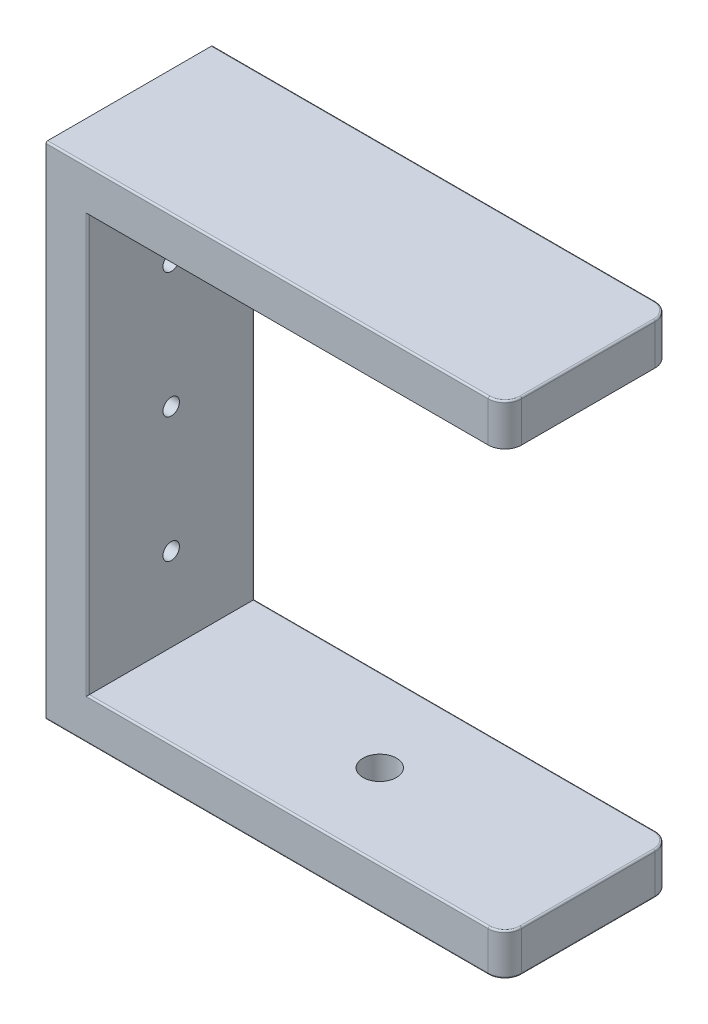
SolidWorks part; units mm, degrees
material "6061-T6 (SS)"
ref_plane "Front Plane" through (0, 0, 0) normal (0, 0, 1) x (1, 0, 0)
ref_plane "Top Plane" through (0, 0, 0) normal (0, 1, 0) x (1, 0, 0)
ref_plane "Right Plane" through (0, 0, 0) normal (1, 0, 0) x (0, 0, -1)
sketch "Sketch1" plane through (0, 0, 0) normal (0, 0, 1) x (1, 0, 0)
  line L0 (69.85, 69.85) -> (69.85, 76.2)
  line L1 (0, 0) -> (69.85, 0)
  line L2 (0, 0) -> (0, 76.2)
  line L3 (0, 76.2) -> (69.85, 76.2)
  line L4 (69.85, 0) -> (69.85, 6.35)
  line L5 (69.85, 69.85) -> (6.35, 69.85)
  line L7 (69.85, 6.35) -> (6.35, 6.35)
  line L8 (6.35, 69.85) -> (6.35, 6.35)
  dimension "D1" = 76.2
  dimension "D2" = 69.85
  dimension "D3" = 6.35
  dimension "D4" = 6.35
  dimension "D5" = 6.35
extrude "Boss-Extrude1" add sketch "Sketch1" along normal blind 25.4
hole_wizard "M3x0.5 Tapped Hole1" positions "Sketch4" profile "Sketch5" tap size "M3x0.5" standard "ANSI Metric" end condition through all
sketch "Sketch4" plane through (0, 0, 0) normal (-1, 0, 0) x (0, 0, 1)
  line L1 (0, 76.2) -> (0, 0) construction
  line L2 (25.4, 76.2) -> (0, 76.2) construction
  point P0 (12.7, 57.15)
  point P4 (12.7, 38.1)
  point P18 (12.7, 19.05)
  dimension "D1" = 19.05
  dimension "D2" = 19.05
  dimension "D3" = 12.7
  dimension "D4" = 19.05
sketch "Sketch5" plane through (0, 57.15, 12.7) normal (0, 1, 0) x (0, 0, 1)
  line L0 (0, 0) -> (0, 69.85)
  line L1 (0, 69.85) -> (1.25, 69.85)
  line L2 (1.25, 69.85) -> (1.25, 0)
  line L5 (1.25, 0) -> (0, 0)
  line L11 (0, -6.35) -> (0, 107.95) construction
  dimension "Thru Tap Drill Dia." = 2.5
  dimension "Thru Tap Drill Depth" = 69.85
cosmetic thread "Hole Thread2" parameters "D2"=3
cosmetic thread "Hole Thread3" parameters "D2"=3
cosmetic thread "Hole Thread4" parameters "D2"=3
sketch "Sketch10" plane through (0, 0, 0) normal (0, -1, 0) x (1, 0, 0)
  line L0 (0, 25.4) -> (0, 0) construction
  line L1 (0, 0) -> (69.85, 0) construction
  point P0 (38.1, 12.7)
  dimension "D1" = 38.1
  dimension "D2" = 12.7
hole_wizard "1/4-20 Tapped Hole1" positions "Sketch11" profile "Sketch12" tap size "1/4-20" standard "ANSI Inch" end condition up to next
sketch "Sketch11" plane through (0, 0, 0) normal (0, -1, 0) x (-1, 0, 0)
  point P0 (-38.1, -12.7)
sketch "Sketch12" plane through (38.1, 0, 12.7) normal (1, 0, 0) x (0, 0, -1)
  line L0 (0, 0) -> (0, 6.35)
  line L1 (0, 6.35) -> (2.5527, 6.35)
  line L2 (2.5527, 6.35) -> (2.5527, 0)
  line L5 (2.5527, 0) -> (0, 0)
  line L11 (0, -6.35) -> (0, 107.95) construction
  dimension "Thru Tap Drill Dia." = 5.1054
  dimension "Thru Tap Drill Depth" = 6.35
cosmetic thread "Hole Thread1" parameters "D2"=6.35
fillet "Fillet1" radius 2.54 4 edges at (69.85, 3.175, 0) (69.85, 3.175, 25.4) (69.85, 73.025, 0) (69.85, 73.025, 25.4)
fillet "Fillet2" radius 0.254 17 edges at (36.83, 6.35, 0) (69.1061, 6.35, 0.7439) (69.85, 6.35, 12.7) (69.1061, 6.35, 24.6561) (33.655, 76.2, 0) (69.1061, 76.2, 0.7439) (69.85, 76.2, 12.7) (69.1061, 76.2, 24.6561) (36.83, 6.35, 25.4) (6.35, 38.1, 25.4) (6.35, 38.1, 0) (33.655, 76.2, 25.4) (33.655, 0, 0) (69.1061, 0, 0.7439) (69.85, 0, 12.7) (69.1061, 0, 24.6561) (33.655, 0, 25.4)
